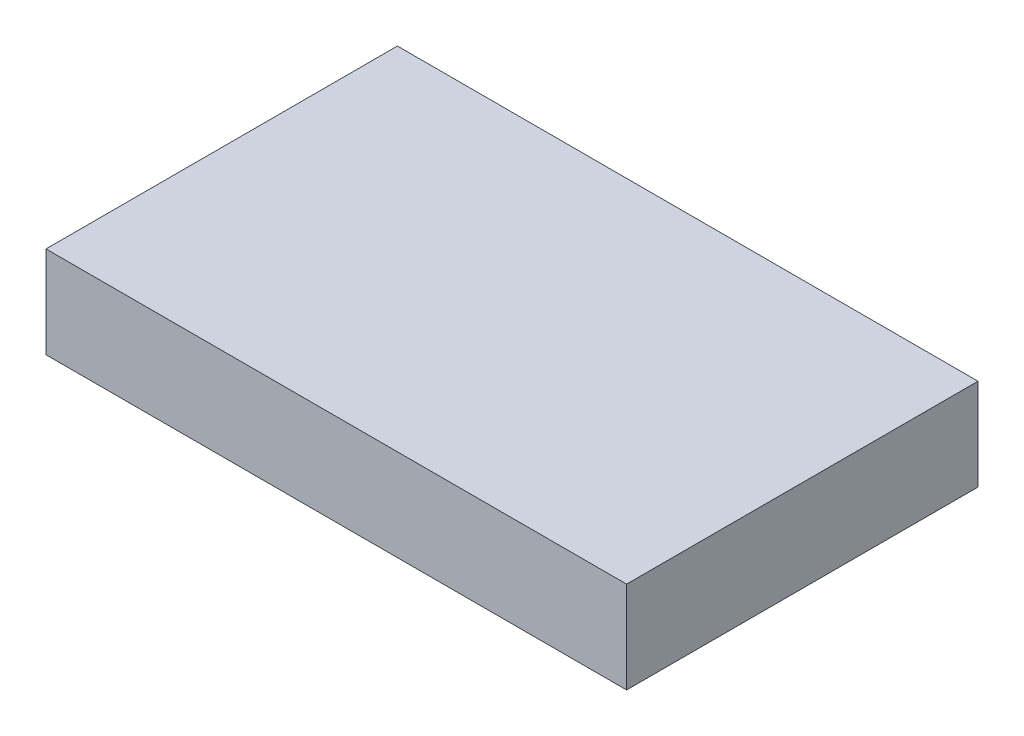
SolidWorks part; units mm, degrees
ref_plane "Front Plane" through (0, 0, 0) normal (0, 0, 1) x (1, 0, 0)
ref_plane "Top Plane" through (0, 0, 0) normal (0, 1, 0) x (1, 0, 0)
ref_plane "Right Plane" through (0, 0, 0) normal (1, 0, 0) x (0, 0, -1)
sketch "Sketch1" plane through (0, 0, 0) normal (0, 1, 0) x (1, 0, 0)
  line L1 (-19, -11.5) -> (19, -11.5)
  line L2 (-19, -11.5) -> (-19, 11.5)
  line L3 (-19, 11.5) -> (19, 11.5)
  line L4 (19, -11.5) -> (19, 11.5)
  line L5 (-19, -11.5) -> (19, 11.5) construction
  line L6 (-19, 11.5) -> (19, -11.5) construction
  point P0 (0, 0)
  dimension "D1" = 38
  dimension "D2" = 23
extrude "Boss-Extrude1" add sketch "Sketch1" along normal blind 6
